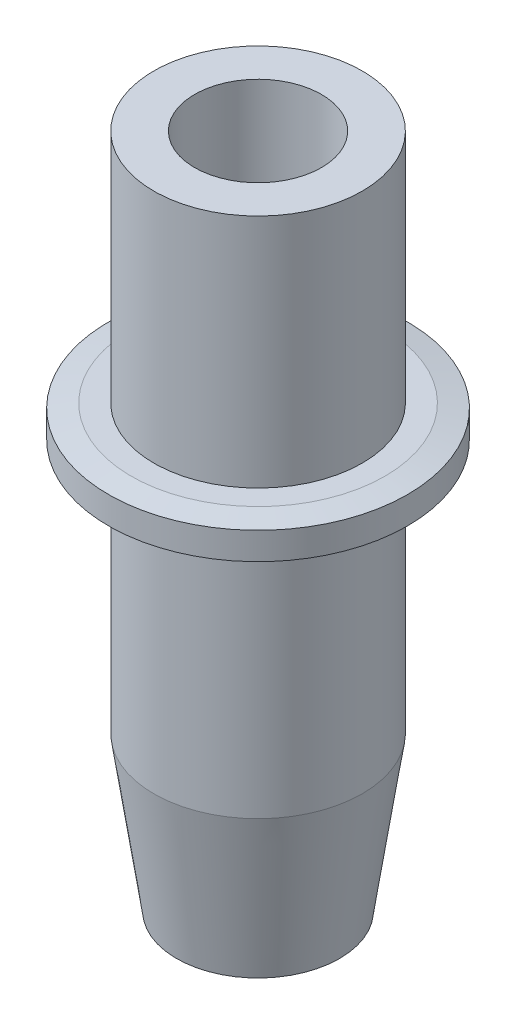
SolidWorks part; units mm, degrees
ref_plane "Front Plane" through (0, 0, 0) normal (0, 0, 1) x (1, 0, 0)
ref_plane "Top Plane" through (0, 0, 0) normal (0, 1, 0) x (1, 0, 0)
ref_plane "Right Plane" through (0, 0, 0) normal (1, 0, 0) x (0, 0, -1)
sketch "Sketch1" plane through (0, 0, 0) normal (0, 0, 1) x (1, 0, 0)
  line L0 (0, -143.9505) -> (0, 7053.5726) construction
  line L1 (0, 0) -> (4.5, 0)
  line L5 (4.5, 0) -> (5.75, 8.5)
  line L6 (5.75, 8.5) -> (5.75, 22.3)
  line L7 (5.75, 22.3) -> (7, 22.3)
  line L8 (7, 22.3) -> (8.25, 22.55)
  line L9 (8.25, 22.55) -> (8.25, 24.05)
  line L10 (8.25, 24.05) -> (7, 24.3)
  line L11 (7, 24.3) -> (5.75, 24.3)
  line L12 (5.75, 24.3) -> (5.75, 37.3)
  line L13 (5.75, 37.3) -> (0, 37.3)
  line L14 (0, 37.3) -> (0, 0)
  point P1 (2.483, 0)
  point P6 (0, 0)
  point P18 (0, 37.3)
  point P29 (0, 0)
  dimension "D2" = 22.3
  dimension "D3" = 11.5
  dimension "D4" = 2
  dimension "D5" = 1.5
  dimension "D6" = 16.5
  dimension "D8" = 8.5
  dimension "D10" = 9
  dimension "D12" = 1.25
  dimension "D13" = 13
revolve "Revolve1" add sketch "Sketch1" angle 360 about L0
sketch "Sketch2" plane through (0, 0, 0) normal (0, 0, 1) x (1, 0, 0)
  line L0 (1.1, 0) -> (1.1, 2)
  line L1 (1.1, 2) -> (2.5, 2)
  line L2 (2.5, 2) -> (2.5, 14.18)
  line L3 (2.5, 14.18) -> (3.5, 14.18)
  line L4 (3.5, 14.18) -> (3.5, 37.3)
  line L5 (3.5, 37.3) -> (0, 37.3)
  line L6 (0, -1000) -> (0, 49000) construction
  line L7 (1.1, 0) -> (0, 0)
  line L8 (5.75, 37.3) -> (-5.75, 37.3) construction
  line L10 (0, 37.3) -> (0, 0)
  dimension "D1" = 7
  dimension "D2" = 14.18
  dimension "D3" = 5
  dimension "D4" = 2.2
  dimension "D5" = 2
revolve "Cut-Revolve1" cut sketch "Sketch2" angle 360 about L6
chamfer "Chamfer1" distance 1 angle 66 1 edges at (2.5, 2, 0)
